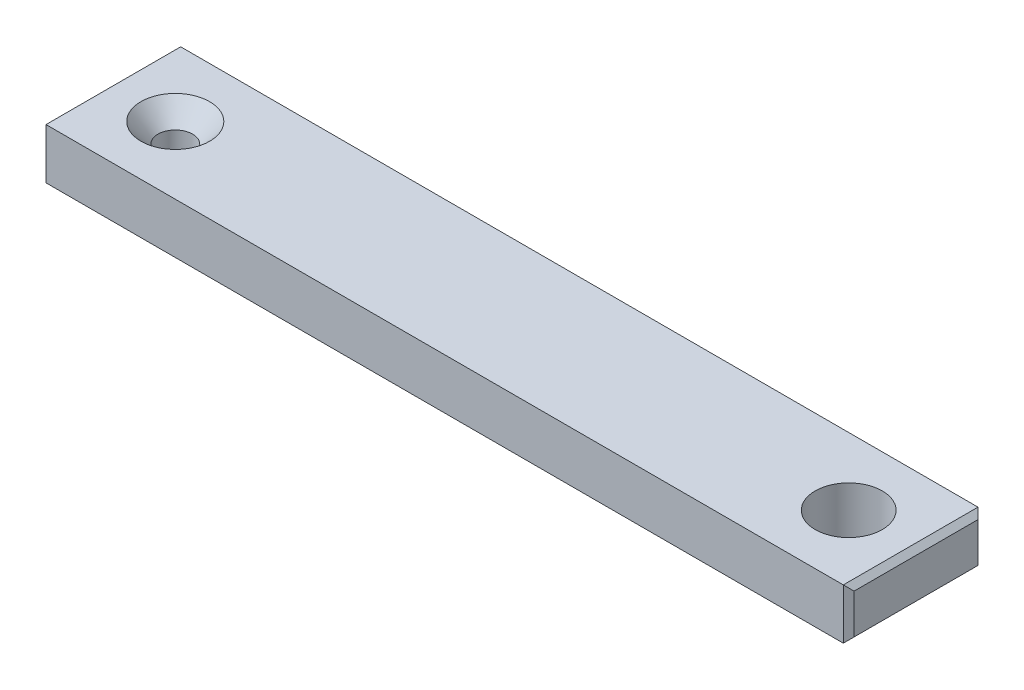
SolidWorks part; units mm, degrees
material "6061-T6 (SS)"
ref_plane "Front Plane" through (0, 0, 0) normal (0, 0, 1) x (1, 0, 0)
ref_plane "Top Plane" through (0, 0, 0) normal (0, 1, 0) x (1, 0, 0)
ref_plane "Right Plane" through (0, 0, 0) normal (1, 0, 0) x (0, 0, -1)
sketch "Sketch1" plane through (0, 0, 0) normal (0, 1, 0) x (1, 0, 0)
  line L0 (-63.5, 0) -> (0, 0) construction
  line L1 (-63.5, 6.35) -> (0, 6.35)
  line L2 (-63.5, -6.35) -> (0, -6.35)
  line L4 (-69.85, 6.35) -> (6.35, 6.35)
  line L5 (-69.85, 6.35) -> (-69.85, -6.35)
  line L6 (-69.85, -6.35) -> (6.35, -6.35)
  line L7 (6.35, 6.35) -> (6.35, -6.35)
  arc A0 (-63.5, 6.35) -> (-63.5, -6.35) centre (-63.5, 0) ccw
  arc A1 (0, -6.35) -> (0, 6.35) centre (0, 0) ccw
  point P2 (-31.75, 0)
  point P9 (-69.85, 0)
  point P10 (6.35, 0)
  dimension "D2" = 76.2
  dimension "D1" = 12.7
extrude "Boss-Extrude2" add sketch "Sketch1" along normal blind 4.7625
sketch "Sketch2" plane through (0, 4.7625, 0) normal (0, 1, 0) x (1, 0, 0)
  line L0 (6.35, 6.35) -> (6.35, -6.35) construction
  line L5 (0, 6.35) -> (0, -6.35)
  line L6 (-69.85, -6.35) -> (6.35, -6.35) construction
  line L7 (-69.85, 6.35) -> (6.35, 6.35) construction
  circle A0 centre (0, 0) radius 3.1623
  point P2 (0, 0)
  dimension "D1" = 6.3246
  dimension "D2" = 6.35
hole_wizard "CSK for #4 Flat Head Socket Cap Screw1" positions "Sketch3" profile "Sketch4" countersink size "#4" standard "ANSI Inch" end condition through all
sketch "Sketch3" plane through (0, 4.7625, 0) normal (0, 1, 0) x (1, 0, 0)
  line L0 (-63.5, 6.35) -> (-63.5, -6.35)
  line L1 (-69.85, 6.35) -> (6.35, 6.35) construction
  line L2 (-69.85, -6.35) -> (6.35, -6.35) construction
  line L4 (-69.85, 6.35) -> (-69.85, -6.35) construction
  point P0 (-63.5, 0)
  point P13 (0, 0)
  point P14 (0, 0)
  dimension "D1" = 6.35
sketch "Sketch4" plane through (-63.5, 4.7625, 0) normal (1, 0, 0) x (0, 0, 1)
  line L0 (0, 0) -> (0, 4.7625)
  line L1 (0, 4.7625) -> (1.6319, 4.7625)
  line L2 (1.6319, 4.7625) -> (1.6319, 1.8481)
  line L3 (1.6319, 1.8481) -> (3.2385, 0)
  line L5 (3.2385, 0) -> (0, 0)
  line L6 (-1.632, 1.8481) -> (-3.2385, 0) construction
  line L11 (0, -6.35) -> (0, 107.95) construction
  dimension "Thru Hole Dia." = 3.2639
  dimension "Thru Hole Depth" = 4.7625
  dimension "Near C'Sink Dia." = 6.477
  dimension "Near C'Sink Angle" = 82
extrude "Cut-Extrude1" cut sketch "Sketch2" against normal through all contours L5 A0 | L5 A0
chamfer "Chamfer1" distance 0.508 angle 45 8 edges at (-69.85, 2.3813, -6.35) (-69.85, 4.7625, 0) (-69.85, 2.3813, 6.35) (-69.85, 0, 0) (6.35, 2.3813, 6.35) (6.35, 4.7625, 0) (6.35, 2.3813, -6.35) (6.35, 0, 0)
